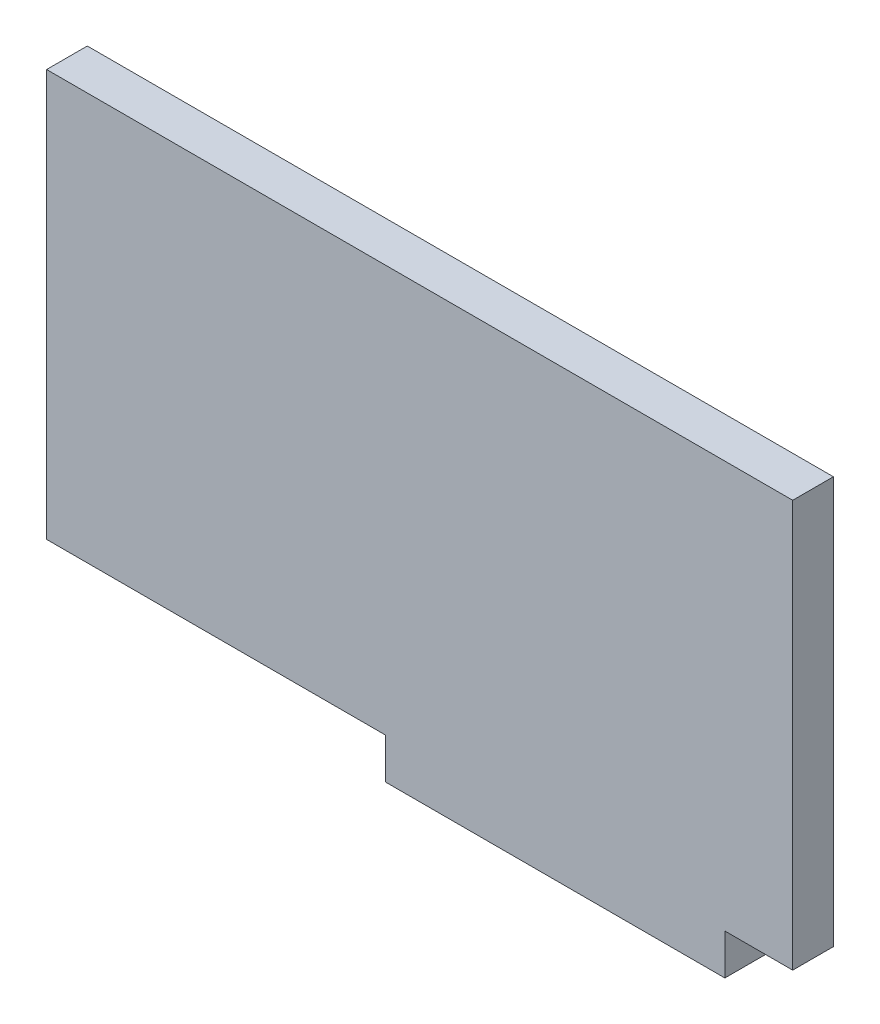
SolidWorks part; units mm, degrees
ref_plane "Plano frontal" through (0, 0, 0) normal (0, 0, 1) x (1, 0, 0)
ref_plane "Plano superior" through (0, 0, 0) normal (0, 1, 0) x (1, 0, 0)
ref_plane "Plano direito" through (0, 0, 0) normal (1, 0, 0) x (0, 0, -1)
sketch "Esboço1" plane through (0, 0, 0) normal (0, 0, 1) x (1, 0, 0)
  line L0 (-7.9412, 1.3698) -> (-2.9412, 1.3698)
  line L1 (-57.9412, 31.3698) -> (-2.9412, 31.3698)
  line L2 (-57.9412, 31.3698) -> (-57.9412, 1.3698)
  line L3 (-57.9412, 1.3698) -> (-32.9412, 1.3698)
  line L4 (-2.9412, 31.3698) -> (-2.9412, 1.3698)
  line L6 (-32.9412, 1.3698) -> (-32.9412, -1.6302)
  line L7 (-32.9412, -1.6302) -> (-7.9412, -1.6302)
  line L8 (-7.9412, 1.3698) -> (-7.9412, -1.6302)
  dimension "D1" = 30
  dimension "D2" = 55
  dimension "D3" = 3
  dimension "D4" = 25
  dimension "D5" = 25
extrude "Ressalto-extrusão1" add sketch "Esboço1" along normal blind 3
